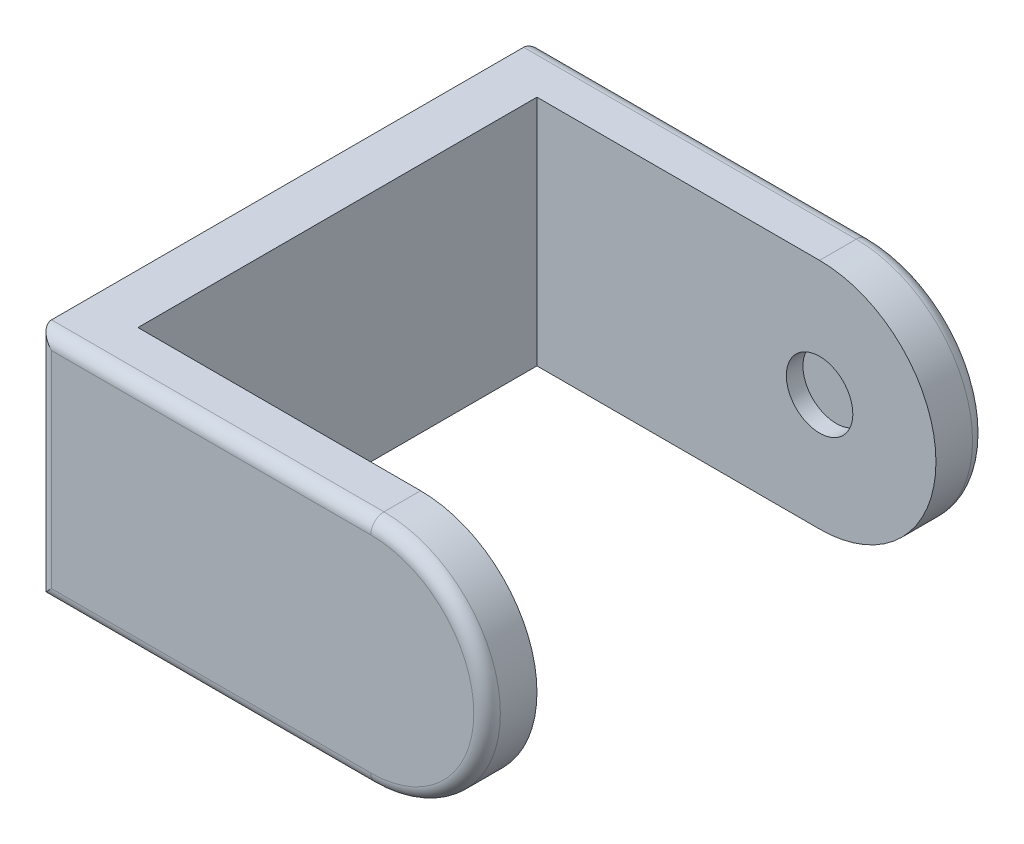
SolidWorks part; units mm, degrees
material "Thornel Mat VMA"
ref_plane "Front Plane" through (0, 0, 0) normal (0, 0, 1) x (1, 0, 0)
ref_plane "Top Plane" through (0, 0, 0) normal (0, 1, 0) x (1, 0, 0)
ref_plane "Right Plane" through (0, 0, 0) normal (1, 0, 0) x (0, 0, -1)
sketch "Sketch1" plane through (0, 0, 0) normal (1, 0, 0) x (0, 0, -1)
  line L1 (-75, -35) -> (75, -35)
  line L2 (-75, -35) -> (-75, 35)
  line L3 (-75, 35) -> (75, 35)
  line L4 (75, -35) -> (75, 35)
  line L5 (-75, -35) -> (75, 35) construction
  line L6 (-75, 35) -> (75, -35) construction
  point P0 (0, 0)
  dimension "D1" = 150
  dimension "D2" = 70
extrude "Boss-Extrude1" add sketch "Sketch1" along normal blind 15
sketch "Sketch2" plane through (15, 0, 0) normal (1, 0, 0) x (0, 0, -1)
  line L0 (-75, 35) -> (-75, -35) construction
  line L1 (-75, 35) -> (-60, 35)
  line L2 (-75, 35) -> (-75, -35)
  line L3 (-75, -35) -> (-60, -35)
  line L4 (-60, 35) -> (-60, -35)
  line L5 (75, 35) -> (-75, 35) construction
  line L6 (-75, -35) -> (75, -35) construction
  line L8 (75, 35) -> (60, 35)
  line L9 (75, 35) -> (75, -35)
  line L10 (75, -35) -> (60, -35)
  line L11 (60, 35) -> (60, -35)
  dimension "D1" = 15
  dimension "D2" = 15
extrude "Boss-Extrude2" add sketch "Sketch2" along normal blind 120
sketch "Sketch3" plane through (0, 0, 75) normal (0, 0, 1) x (1, 0, 0)
  line L0 (135, 35) -> (135, -35) construction
  line L1 (135, -35) -> (0, -35) construction
  line L2 (135, 35) -> (0, 35) construction
  line L3 (135, -35) -> (0, -35)
  line L4 (135, 35) -> (135, -35)
  line L5 (135, 35) -> (0, 35)
  circle A0 centre (100, 0) radius 35
  point P2 (98.4139, 0)
  line M4 (135, -35) -> (135, 35)
  line M5 (135, 35) -> (0, 35)
  dimension "D1" = 70
extrude "Cut-Extrude1" cut sketch "Sketch3" against normal through all contours A0 L4 M5 | A0 L3 M4
sketch "Sketch5" plane through (0, 0, 60) normal (0, 0, -1) x (-1, 0, 0)
  circle A0 centre (-100, 0) radius 10
  point P2 (0, 0)
  dimension "D1" = 20
extrude "Cut-Extrude2" cut sketch "Sketch5" against normal blind 5 and the other way blind 125
fillet "Fillet1" radius 4 8 edges at (50, 35, -75) (0, 0, -75) (50, -35, -75) (135, 0, -75) (0, 0, 75) (50, 35, 75) (135, 0, 75) (50, -35, 75)
sketch "Sketch6" plane through (0, 0, 0) normal (-1, 0, 0) x (0, 0, 1)
  circle A0 centre (0, 0) radius 15
  dimension "D1" = 30
extrude "Cut-Extrude3" cut sketch "Sketch6" against normal blind 5
